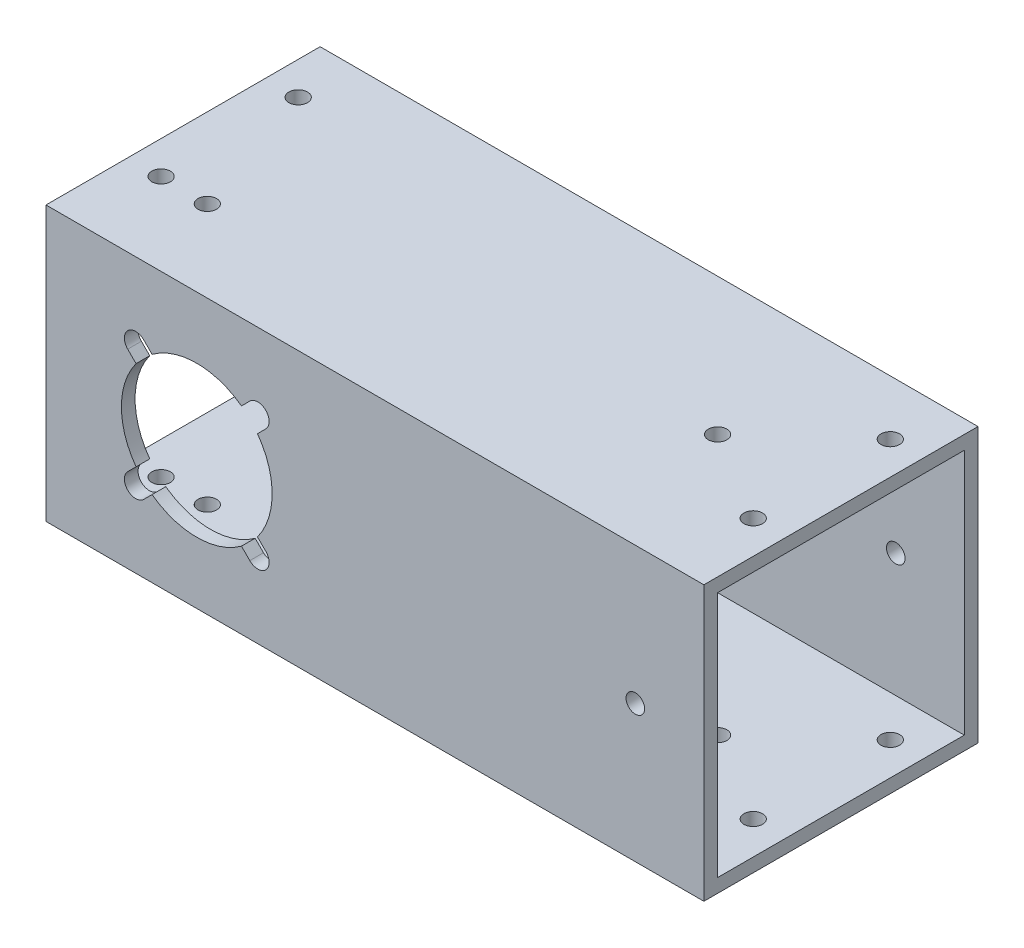
SolidWorks part; units mm, degrees
material "6061-T6 (SS)"
ref_plane "Front Plane" through (0, 0, 0) normal (0, 0, 1) x (1, 0, 0)
ref_plane "Top Plane" through (0, 0, 0) normal (0, 1, 0) x (1, 0, 0)
ref_plane "Right Plane" through (0, 0, 0) normal (1, 0, 0) x (0, 0, -1)
sketch "Sketch1" plane through (0, 0, 0) normal (1, 0, 0) x (0, 0, -1)
  line L1 (-31.75, -31.75) -> (31.75, -31.75)
  line L2 (-31.75, -31.75) -> (-31.75, 31.75)
  line L3 (-31.75, 31.75) -> (31.75, 31.75)
  line L4 (31.75, -31.75) -> (31.75, 31.75)
  point P0 (0, 0)
  dimension "D1" = 63.5
extrude "Boss-Extrude1" add sketch "Sketch1" along normal blind 704.85
sketch "Sketch2" plane through (704.85, 0, 0) normal (1, 0, 0) x (0, 0, -1)
  line L0 (31.75, 31.75) -> (-31.75, 31.75) construction
  line L1 (-28.575, -28.575) -> (28.575, -28.575)
  line L2 (-28.575, -28.575) -> (-28.575, 28.575)
  line L3 (-28.575, 28.575) -> (28.575, 28.575)
  line L4 (28.575, -28.575) -> (28.575, 28.575)
  line L5 (-28.575, -28.575) -> (28.575, 28.575) construction
  line L6 (-28.575, 28.575) -> (28.575, -28.575) construction
  point P0 (0, 0)
  dimension "D1" = 3.175
extrude "Cut-Extrude1" cut sketch "Sketch2" against normal through all
sketch "Sketch3" plane through (0, 0, 31.75) normal (0, 0, 1) x (1, 0, 0)
  line L0 (0, 0) -> (704.85, 0) construction
  line L1 (704.85, 31.75) -> (704.85, -31.75) construction
  line L2 (352.425, -31.75) -> (352.425, 31.75) construction
  line L3 (704.85, -31.75) -> (0, -31.75) construction
  line L4 (704.85, 31.75) -> (0, 31.75) construction
  circle A0 centre (352.425, 0) radius 17.4625
  circle A1 centre (34.925, 0) radius 17.4625
  circle A2 centre (669.925, 0) radius 17.4625
  dimension "D1" = 34.925
  dimension "D2" = 317.5
  dimension "D3" = 317.5
extrude "Cut-Extrude2" cut sketch "Sketch3" against normal up to next
sketch "Sketch8" plane through (0, 31.75, 0) normal (0, 1, 0) x (1, 0, 0)
  line L0 (0, 0) -> (704.85, 0) construction
  line L1 (704.85, 31.75) -> (704.85, -31.75) construction
  line L2 (352.425, 0) -> (352.425, 31.75) construction
  line L3 (704.85, 31.75) -> (0, 31.75) construction
  circle A0 centre (466.725, 0) radius 2.1526
  circle A1 centre (123.825, 0) radius 2.1526
  circle A2 centre (581.025, 0) radius 2.1526
  circle A3 centre (238.125, 0) radius 2.1526
  dimension "D1" = 4.3053
  dimension "D2" = 114.3
  dimension "D3" = 228.6
extrude "Cut-Extrude6" cut sketch "Sketch8" against normal through all
sketch "Sketch10" plane through (0, 0, 31.75) normal (0, 0, 1) x (1, 0, 0)
  line L0 (0, 0) -> (704.85, 0) construction
  line L1 (704.85, 31.75) -> (704.85, -31.75) construction
  line L2 (352.425, 0) -> (352.425, 31.75) construction
  line L3 (704.85, 31.75) -> (0, 31.75) construction
  circle A0 centre (225.425, 0) radius 2.1527
  circle A1 centre (568.325, 0) radius 2.1526
  circle A2 centre (136.525, 0) radius 2.1527
  circle A3 centre (479.425, 0) radius 2.1526
  dimension "D1" = 4.3053
  dimension "D2" = 127
  dimension "D3" = 215.9
extrude "Cut-Extrude7" cut sketch "Sketch10" against normal through all
sketch "Sketch13" plane through (0, 0, -31.75) normal (0, 0, -1) x (-1, 0, 0)
  line L0 (0, 0) -> (-704.85, 0) construction
  line L1 (-704.85, -31.75) -> (-704.85, 31.75) construction
  line L2 (-352.425, 0) -> (-34.925, 0) construction
  line L3 (-352.425, 0) -> (-669.925, 0) construction
  circle A0 centre (-352.425, 0) radius 16
  circle A1 centre (-34.925, 0) radius 16
  circle A2 centre (-669.925, 0) radius 16
  dimension "D3" = 32
  dimension "D1" = 317.5
  dimension "D2" = 317.5
extrude "Cut-Extrude9" cut sketch "Sketch13" against normal up to next
sketch "Sketch14" plane through (0, 0, -31.75) normal (0, 0, -1) x (-1, 0, 0)
  line L0 (0, 0) -> (-704.85, 0) construction
  line L1 (-704.85, -31.75) -> (-704.85, 31.75) construction
  line L2 (-352.425, 0) -> (-34.925, 0) construction
  line L3 (-669.925, 0) -> (-352.425, 0) construction
  line L4 (-352.425, 0) -> (-338.2829, 14.1421) construction
  line L5 (-669.925, 0) -> (-655.7829, 14.1421) construction
  line L6 (-34.925, 0) -> (-20.7829, 14.1421) construction
  line L7 (-352.425, 0) -> (-338.2829, -14.1421) construction
  line L8 (-352.425, 0) -> (-366.5671, -14.1421) construction
  line L9 (-352.425, 0) -> (-366.5671, 14.1421) construction
  line L10 (-34.925, 0) -> (-20.7829, -14.1421) construction
  line L11 (-34.925, 0) -> (-49.0671, -14.1421) construction
  line L12 (-34.925, 0) -> (-49.0671, 14.1421) construction
  line L13 (-669.925, 0) -> (-655.7829, -14.1421) construction
  line L14 (-669.925, 0) -> (-684.0671, -14.1421) construction
  line L15 (-669.925, 0) -> (-684.0671, 14.1421) construction
  circle A0 centre (-655.7829, 14.1421) radius 2.625
  circle A1 centre (-338.2829, 14.1421) radius 2.625
  circle A2 centre (-20.7829, 14.1421) radius 2.625
  circle A3 centre (-352.425, 0) radius 16
  circle A4 centre (-34.925, 0) radius 16
  circle A5 centre (-669.925, 0) radius 16
  circle A6 centre (-338.2829, -14.1421) radius 2.625
  circle A7 centre (-366.5671, -14.1421) radius 2.625
  circle A8 centre (-366.5671, 14.1421) radius 2.625
  circle A9 centre (-20.7829, -14.1421) radius 2.625
  circle A10 centre (-49.0671, -14.1421) radius 2.625
  circle A11 centre (-49.0671, 14.1421) radius 2.625
  circle A12 centre (-655.7829, -14.1421) radius 2.625
  circle A13 centre (-684.0671, -14.1421) radius 2.625
  circle A14 centre (-684.0671, 14.1421) radius 2.625
  point P28 (-352.425, 0)
  point P35 (-34.925, 0)
  point P42 (-669.925, 0)
  dimension "D4" = 5.25
  dimension "D1" = 45
  dimension "D2" = 45
  dimension "D3" = 45
  dimension "D5" = 20
  dimension "D6" = 4
  dimension "D7" = 4
  dimension "D8" = 4
extrude "Cut-Extrude10" cut sketch "Sketch14" against normal up to next (3.175 mm away)
sketch "Sketch15" plane through (0, 0, 31.75) normal (0, 0, 1) x (1, 0, 0)
  line L0 (0, 0) -> (704.85, 0) construction
  line L1 (50.9233, 12.286) -> (47.211, 15.9983) construction
  line L2 (0, 31.75) -> (0, -31.75) construction
  line L3 (704.85, 31.75) -> (704.85, -31.75) construction
  line L4 (352.425, 0) -> (352.425, 31.75) construction
  line L5 (704.85, 31.75) -> (0, 31.75) construction
  line L6 (34.925, 0) -> (352.425, 0) construction
  line L7 (193.675, 0) -> (193.675, 31.75) construction
  line L8 (669.925, 0) -> (352.425, 0) construction
  line L9 (511.175, 0) -> (511.175, 31.75) construction
  line L10 (352.425, 0) -> (366.5671, 14.1421) construction
  line L11 (364.711, -15.9983) -> (362.7764, -14.0637)
  line L12 (49.0671, 14.1421) -> (50.9233, 12.286) construction
  line L13 (366.5671, 14.1421) -> (364.711, 15.9983) construction
  line L14 (364.711, 15.9983) -> (368.4233, 12.286) construction
  line L15 (368.4233, 12.286) -> (366.4887, 10.3514)
  line L16 (364.711, 15.9983) -> (362.7764, 14.0637)
  line L17 (368.4233, -12.286) -> (366.4887, -10.3514)
  line L18 (352.425, 0) -> (366.5671, -14.1421) construction
  line L19 (366.5671, -14.1421) -> (368.4233, -12.286) construction
  line L20 (368.4233, -12.286) -> (364.711, -15.9983) construction
  line L21 (336.4267, -12.286) -> (338.3613, -10.3514)
  line L22 (340.139, -15.9983) -> (342.0736, -14.0637)
  line L23 (352.425, 0) -> (338.2829, -14.1421) construction
  line L24 (338.2829, -14.1421) -> (340.139, -15.9983) construction
  line L25 (340.139, -15.9983) -> (336.4267, -12.286) construction
  line L26 (340.139, 15.9983) -> (342.0736, 14.0637)
  line L27 (336.4267, 12.286) -> (338.3613, 10.3514)
  line L28 (352.425, 0) -> (338.2829, 14.1421) construction
  line L29 (338.2829, 14.1421) -> (336.4267, 12.286) construction
  line L30 (336.4267, 12.286) -> (340.139, 15.9983) construction
  line L31 (34.925, 0) -> (49.0671, 14.1421) construction
  line L32 (47.211, -15.9983) -> (50.9233, -12.286) construction
  line L33 (49.0671, -14.1421) -> (47.211, -15.9983) construction
  line L34 (34.925, 0) -> (49.0671, -14.1421) construction
  line L35 (18.9267, -12.286) -> (22.639, -15.9983) construction
  line L36 (20.7829, -14.1421) -> (18.9267, -12.286) construction
  line L37 (34.925, 0) -> (20.7829, -14.1421) construction
  line L38 (22.639, 15.9983) -> (18.9267, 12.286) construction
  line L39 (20.7829, 14.1421) -> (22.639, 15.9983) construction
  line L40 (34.925, 0) -> (20.7829, 14.1421) construction
  line L41 (34.925, 0) -> (34.925, 31.75) construction
  line L42 (50.9233, 12.286) -> (48.9887, 10.3514)
  line L43 (47.211, 15.9983) -> (45.2764, 14.0637)
  line L44 (47.211, -15.9983) -> (45.2764, -14.0637)
  line L45 (50.9233, -12.286) -> (48.9887, -10.3514)
  line L46 (18.9267, -12.286) -> (20.8613, -10.3514)
  line L47 (22.639, 15.9983) -> (24.5736, 14.0637)
  line L48 (18.9267, 12.286) -> (20.8613, 10.3514)
  line L49 (22.639, -15.9983) -> (24.5736, -14.0637)
  line L50 (685.9233, 12.286) -> (682.211, 15.9983) construction
  line L51 (684.0671, 14.1421) -> (685.9233, 12.286) construction
  line L52 (669.925, 0) -> (684.0671, 14.1421) construction
  line L53 (682.211, -15.9983) -> (685.9233, -12.286) construction
  line L54 (684.0671, -14.1421) -> (682.211, -15.9983) construction
  line L55 (669.925, 0) -> (684.0671, -14.1421) construction
  line L56 (653.9267, -12.286) -> (657.639, -15.9983) construction
  line L57 (655.7829, -14.1421) -> (653.9267, -12.286) construction
  line L58 (669.925, 0) -> (655.7829, -14.1421) construction
  line L59 (657.639, 15.9983) -> (653.9267, 12.286) construction
  line L60 (655.7829, 14.1421) -> (657.639, 15.9983) construction
  line L61 (669.925, 0) -> (655.7829, 14.1421) construction
  line L62 (669.925, 0) -> (669.925, 31.75) construction
  line L63 (685.9233, 12.286) -> (683.9887, 10.3514)
  line L64 (682.211, 15.9983) -> (680.2764, 14.0637)
  line L65 (682.211, -15.9983) -> (680.2764, -14.0637)
  line L66 (685.9233, -12.286) -> (683.9887, -10.3514)
  line L67 (653.9267, -12.286) -> (655.8613, -10.3514)
  line L68 (657.639, 15.9983) -> (659.5736, 14.0637)
  line L69 (653.9267, 12.286) -> (655.8613, 10.3514)
  line L70 (657.639, -15.9983) -> (659.5736, -14.0637)
  arc A0 (362.7764, 14.0637) -> (342.0736, 14.0637) centre (352.425, 0) ccw
  arc A1 (368.4233, 12.286) -> (364.711, 15.9983) centre (366.5671, 14.1421) ccw
  arc A2 (364.711, -15.9983) -> (368.4233, -12.286) centre (366.5671, -14.1421) ccw
  arc A3 (336.4267, -12.286) -> (340.139, -15.9983) centre (338.2829, -14.1421) ccw
  arc A4 (340.139, 15.9983) -> (336.4267, 12.286) centre (338.2829, 14.1421) ccw
  arc A5 (338.3613, 10.3514) -> (338.3613, -10.3514) centre (352.425, 0) ccw
  arc A6 (342.0736, -14.0637) -> (362.7764, -14.0637) centre (352.425, 0) ccw
  arc A7 (366.4887, -10.3514) -> (366.4887, 10.3514) centre (352.425, 0) ccw
  arc A8 (20.8613, -10.3514) -> (20.8613, 10.3514) centre (34.925, 0) cw
  arc A9 (45.2764, -14.0637) -> (24.5736, -14.0637) centre (34.925, 0) cw
  arc A10 (48.9887, 10.3514) -> (48.9887, -10.3514) centre (34.925, 0) cw
  arc A11 (47.211, 15.9983) -> (50.9233, 12.286) centre (49.0671, 14.1421) cw
  arc A13 (50.9233, -12.286) -> (47.211, -15.9983) centre (49.0671, -14.1421) cw
  arc A14 (22.639, -15.9983) -> (18.9267, -12.286) centre (20.7829, -14.1421) cw
  arc A15 (18.9267, 12.286) -> (22.639, 15.9983) centre (20.7829, 14.1421) cw
  arc A16 (24.5736, 14.0637) -> (45.2764, 14.0637) centre (34.925, 0) cw
  arc A17 (655.8613, -10.3514) -> (655.8613, 10.3514) centre (669.925, 0) cw
  arc A18 (680.2764, -14.0637) -> (659.5736, -14.0637) centre (669.925, 0) cw
  arc A19 (683.9887, 10.3514) -> (683.9887, -10.3514) centre (669.925, 0) cw
  arc A20 (682.211, 15.9983) -> (685.9233, 12.286) centre (684.0671, 14.1421) cw
  arc A21 (685.9233, -12.286) -> (682.211, -15.9983) centre (684.0671, -14.1421) cw
  arc A22 (657.639, -15.9983) -> (653.9267, -12.286) centre (655.7829, -14.1421) cw
  arc A23 (653.9267, 12.286) -> (657.639, 15.9983) centre (655.7829, 14.1421) cw
  arc A24 (659.5736, 14.0637) -> (680.2764, 14.0637) centre (669.925, 0) cw
  point P43 (352.425, 0)
  dimension "D2" = 45
  dimension "D3" = 5.25
  dimension "D7" = 17.4625
  dimension "D1" = 20
  dimension "D4" = 90
  dimension "D5" = 5.25
  dimension "D8" = 2.7359
  dimension "D6" = 4
extrude "Cut-Extrude11" cut sketch "Sketch15" against normal up to next
sketch "Sketch17" plane through (0, -31.75, 0) normal (0, -1, 0) x (1, 0, 0)
  line L0 (0, 0) -> (704.85, 0) construction
  line L1 (704.85, 31.75) -> (704.85, -31.75) construction
  line L2 (342.9, 0) -> (361.95, 0)
  line L3 (342.9, -25.4) -> (361.95, -25.4)
  line L4 (342.9, -25.4) -> (342.9, 0)
  line L6 (361.95, -25.4) -> (361.95, 0)
  line L7 (342.9, -25.4) -> (352.425, 0) construction
  line L8 (352.425, 0) -> (361.95, -25.4) construction
  point P5 (352.425, 0)
extrude "Cut-Extrude13" cut sketch "Sketch17" against normal up to next
sketch "Sketch18" plane through (704.85, 0, 0) normal (1, 0, 0) x (0, 0, -1)
  line L1 (-31.75, 31.75) -> (31.75, 31.75)
  line L2 (-31.75, 31.75) -> (-31.75, -31.75)
  line L3 (-31.75, -31.75) -> (31.75, -31.75)
  line L4 (31.75, 31.75) -> (31.75, -31.75)
extrude "Cut-Extrude14" cut sketch "Sketch18" against normal blind 552.45
hole_wizard "#8 Clearance Hole1" positions "Sketch20" profile "Sketch19" hole size "#8" standard "ANSI Inch" end condition through all
sketch "Sketch20" plane through (0, 31.75, 0) normal (0, 1, 0) x (1, 0, 0)
  line L0 (152.4, 31.75) -> (0, 31.75) construction
  line L1 (0, 31.75) -> (0, -31.75) construction
  line L2 (152.4, -31.75) -> (0, -31.75) construction
  line L3 (152.4, 31.75) -> (152.4, -31.75) construction
  point P0 (7.62, 19.05)
  point P2 (7.62, -12.7)
  point P4 (144.78, -12.7)
  point P6 (144.78, 19.05)
  dimension "D1" = 12.7
  dimension "D2" = 7.62
  dimension "D3" = 7.62
  dimension "D4" = 19.05
  dimension "D5" = 7.62
  dimension "D6" = 7.62
  dimension "D7" = 12.7
  dimension "D8" = 19.05
sketch "Sketch19" plane through (7.62, 31.75, -19.05) normal (1, 0, 0) x (0, 0, 1)
  line L0 (0, 0) -> (0, 63.5)
  line L1 (0, 63.5) -> (2.1526, 63.5)
  line L2 (2.1526, 63.5) -> (2.1526, 0)
  line L5 (2.1526, 0) -> (0, 0)
  line L11 (0, -6.35) -> (0, 107.95) construction
  dimension "Thru Hole Dia." = 4.3053
  dimension "Thru Hole Depth" = 63.5
sketch "Sketch21" plane through (0, -31.75, 0) normal (0, -1, 0) x (-1, 0, 0)
  circle A0 centre (-18.4785, -12.8587) radius 2.1527
extrude "Cut-Extrude15" cut sketch "Sketch21" against normal blind 6.35
sketch "Sketch23" plane through (0, 28.575, 0) normal (0, -1, 0) x (-1, 0, 0)
  circle A0 centre (-18.4785, -12.8587) radius 2.1527
extrude "Cut-Extrude16" cut sketch "Sketch23" against normal blind 13.97
